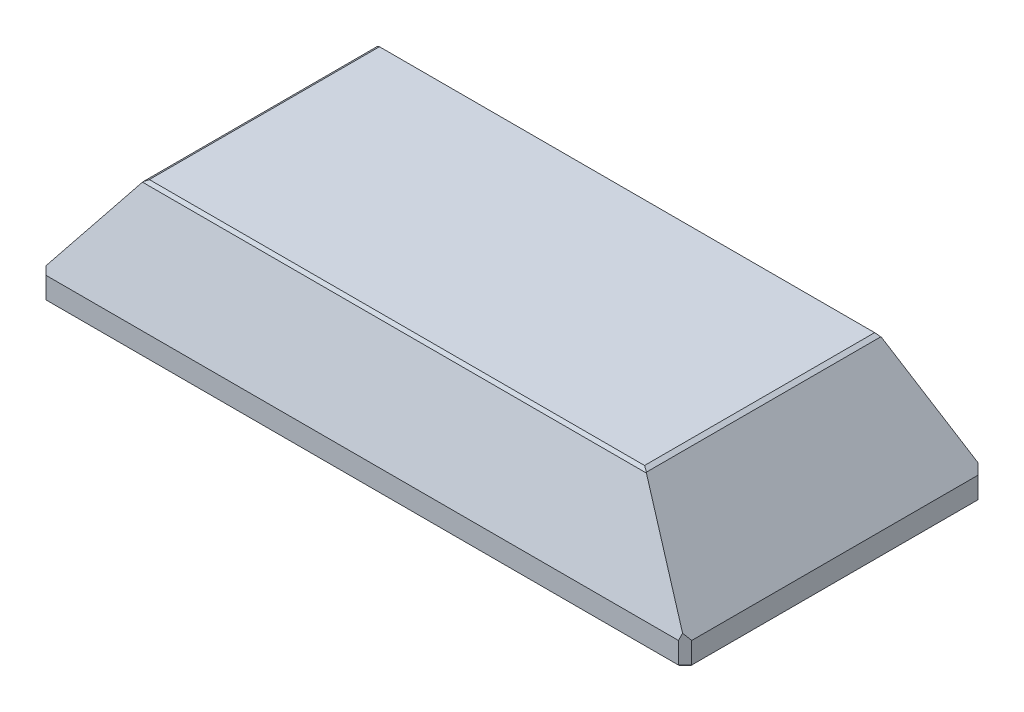
SolidWorks part; units mm, degrees
ref_plane "Front Plane" through (0, 0, 0) normal (0, 0, 1) x (1, 0, 0)
ref_plane "Top Plane" through (0, 0, 0) normal (0, 1, 0) x (1, 0, 0)
ref_plane "Right Plane" through (0, 0, 0) normal (1, 0, 0) x (0, 0, -1)
sketch "Sketch1" plane through (0, 0, 0) normal (0, 1, 0) x (1, 0, 0)
  line L1 (-97, -45) -> (97, -45)
  line L2 (-97, -45) -> (-97, 45)
  line L3 (-97, 45) -> (97, 45)
  line L4 (97, -45) -> (97, 45)
  line L5 (-97, -45) -> (97, 45) construction
  line L6 (-97, 45) -> (97, -45) construction
  point P0 (0, 0)
  dimension "D1" = 194
  dimension "D2" = 90
ref_plane "Plane1" through (0, 37, 0) normal (0, 1, 0) x (1, 0, 0)
sketch "Sketch2" plane through (0, 37, 0) normal (0, 1, 0) x (1, 0, 0)
  line L1 (-75, -35) -> (75, -35)
  line L2 (-75, -35) -> (-75, 35)
  line L3 (-75, 35) -> (75, 35)
  line L4 (75, -35) -> (75, 35)
  line L5 (-75, -35) -> (75, 35) construction
  line L6 (-75, 35) -> (75, -35) construction
  point P0 (0, 0)
  dimension "D1" = 70
  dimension "D2" = 150
extrude "Boss-Extrude1" add sketch "Sketch1" along normal blind 7
sketch "Sketch3" plane through (0, 7, 0) normal (0, 1, 0) x (1, 0, 0)
  line L4 (97, -45) -> (97, 45)
  line L5 (97, 45) -> (-97, 45)
  line L6 (-97, 45) -> (-97, -45)
  line L7 (-97, -45) -> (97, -45)
  line L8 (97, -45) -> (97, 45)
  line L9 (97, 45) -> (-97, 45)
  line L10 (-97, 45) -> (-97, -45)
  line L11 (-97, -45) -> (97, -45)
  dimension "D1" = 0
loft "Loft2" add profiles "Sketch3", "Sketch2"
chamfer "Chamfer1" distance 2 angle 45 4 edges at (-97, 3.5, 45) (97, 3.5, 45) (97, 3.5, -45) (-97, 3.5, -45)
sketch "Sketch4" plane through (0, 0, 0) normal (0, -1, 0) x (1, 0, 0)
  line L0 (0, 45) -> (0, -45) construction
  line L1 (-95, 45) -> (95, 45) construction
  line L2 (95, -45) -> (-95, -45) construction
  line L3 (-40, -41.5) -> (40, -41.5) construction
  circle A0 centre (40, -41.5) radius 2.15
  circle A1 centre (-40, -41.5) radius 2.15
  point P9 (0, -41.5)
  dimension "D3" = 4.3
  dimension "D1" = 3.5
  dimension "D2" = 80
extrude "Cut-Extrude1" cut sketch "Sketch4" against normal blind 7
sketch "Sketch5" plane through (0, 0, 0) normal (0, -1, 0) x (1, 0, 0)
  line L1 (-75, -30) -> (75, -30)
  line L2 (-75, -30) -> (-75, 30)
  line L3 (-75, 30) -> (75, 30)
  line L4 (75, -30) -> (75, 30)
  line L5 (-75, -30) -> (75, 30) construction
  line L6 (-75, 30) -> (75, -30) construction
  point P0 (0, 0)
  dimension "D1" = 60
  dimension "D2" = 150
extrude "Cut-Extrude2" cut sketch "Sketch5" against normal offset from surface (36 mm away) 1 up to face at (0, 37, 0)
mirror "Mirror1" about plane through (0, 0, 0) normal (0, 0, 1) of "Cut-Extrude1"
sketch "Sketch6" plane through (0, 0, 0) normal (0, -1, 0) x (1, 0, 0)
  line L0 (75, 30) -> (75, -30) construction
  line L1 (-75, -32) -> (75, -32)
  line L2 (-75, -32) -> (-75, 32)
  line L3 (-75, 32) -> (75, 32)
  line L4 (75, -32) -> (75, 32)
  line L5 (-75, -32) -> (75, 32) construction
  line L6 (-75, 32) -> (75, -32) construction
  line L7 (75, 30) -> (-75, 30) construction
  point P0 (0, 0)
  dimension "D1" = 2
extrude "Cut-Extrude3" cut sketch "Sketch6" against normal offset from surface (32 mm away) 4 up to face at (0, 36, 0)
sketch "Sketch7" plane through (0, 0, 0) normal (0, -1, 0) x (1, 0, 0)
  line L0 (-75, -32) -> (75, -32) construction
  line L1 (-75, 32) -> (-81, 32)
  line L2 (-75, 32) -> (-75, -32)
  line L3 (-75, -32) -> (-81, -32)
  line L4 (-81, 32) -> (-81, -32)
  line L5 (0, 45) -> (0, -45) construction
  line L6 (-95, 45) -> (95, 45) construction
  line L7 (95, -45) -> (-95, -45) construction
  line L8 (81, 32) -> (81, -32)
  line L9 (75, -32) -> (81, -32)
  line L10 (75, 32) -> (75, -32)
  line L11 (75, 32) -> (81, 32)
  dimension "D1" = 6
extrude "Cut-Extrude4" cut sketch "Sketch7" against normal blind 4
sketch "Sketch8" plane through (0, 4, 0) normal (0, -1, 0) x (1, 0, 0)
  line L0 (-81, 0) -> (81, 0) construction
  line L1 (-81, 32) -> (-81, -32) construction
  line L2 (81, -32) -> (81, 32) construction
  line L3 (-78, -25) -> (-78, 25) construction
  line L4 (-81, 32) -> (-75, -32) construction
  line L5 (0, 32) -> (0, -32) construction
  line L6 (-75, 32) -> (75, 32) construction
  line L7 (-81, -32) -> (81, -32) construction
  circle A0 centre (-78, 25) radius 2.05
  circle A1 centre (-78, -25) radius 2.05
  circle A2 centre (78, -25) radius 2.05
  circle A3 centre (78, 25) radius 2.05
  point P9 (-78, 0)
  dimension "D1" = 4.1
  dimension "D2" = 50
extrude "Cut-Extrude5" cut sketch "Sketch8" against normal blind 6
chamfer "Chamfer2" distance 1 angle 20 4 edges
chamfer "Chamfer3" distance 0.6 angle 45 8 edges at (96, 0, -44) (97, 0, 0) (96, 0, 44) (0, 0, -45) (-96, 0, -44) (-97, 0, 0) (-96, 0, 44) (0, 0, 45)
sketch "Skizze1" plane through (0, 36, 0) normal (0, -1, 0) x (1, 0, 0)
  line L0 (0, 30) -> (0, -25) construction
  line L1 (-75, 30) -> (75, 30) construction
  line L2 (-75, 30) -> (75, 30) construction
  line L3 (75, 0) -> (-75, 0) construction
  line L4 (75, 30) -> (75, -30) construction
  line L5 (-75, -32) -> (-75, 32) construction
  line L6 (-27.0252, -17.5) -> (27.0252, -17.5)
  line L7 (-27.0252, 30) -> (27.0252, 30)
  line L8 (-27.0252, 30) -> (-27.0252, 17.5)
  line L9 (-27.0252, 17.5) -> (27.0252, 17.5)
  line L10 (27.0252, 30) -> (27.0252, 17.5)
  line L11 (27.0252, -30) -> (27.0252, -17.5)
  line L12 (-27.0252, -30) -> (27.0252, -30)
  line L13 (-27.0252, -30) -> (-27.0252, -17.5)
  line L14 (75, 32) -> (75, -32) construction
  line L15 (75, 10.7265) -> (35, 10.7265)
  line L16 (75, 10.7265) -> (75, -10.7265)
  line L17 (75, -10.7265) -> (35, -10.7265)
  line L18 (35, 10.7265) -> (35, -10.7265)
  line L23 (-75, -30) -> (-75, 30) construction
  point P29 (0, 17.5)
  dimension "D1" = 35
  dimension "D2" = 110
extrude "Aufsatz-Linear austragen1" add sketch "Skizze1" along normal blind 10
sketch "Skizze3" plane through (0, 36, 0) normal (0, -1, 0) x (-1, 0, 0)
  line L0 (75, -30) -> (75, -32) construction
  line L2 (75, -31) -> (75, -30)
  line L10 (27.0252, -30) -> (27.0252, -31)
  line L11 (27.0252, -31) -> (75, -31)
  line L12 (27.0252, -30) -> (75, -30)
  line L14 (0, -44.4) -> (0, 44.4) construction
  line L22 (-94.7515, -44.4) -> (94.7515, -44.4) construction
  line L23 (94.7515, 44.4) -> (-94.7515, 44.4) construction
  line L24 (96.4, 0) -> (-96.4, 0) construction
  line L25 (96.4, -42.7515) -> (96.4, 42.7515) construction
  line L26 (-96.4, 42.7515) -> (-96.4, -42.7515) construction
  line L27 (-27.0252, -30) -> (-27.0252, -31)
  line L28 (-27.0252, -30) -> (-75, -30)
  line L29 (-27.0252, -31) -> (-75, -31)
  line L30 (-75, -31) -> (-75, -30)
  line L31 (27.0252, 30) -> (27.0252, 31)
  line L32 (27.0252, 31) -> (75, 31)
  line L33 (27.0252, 30) -> (75, 30)
  line L34 (75, 31) -> (75, 30)
  line L35 (-75, 31) -> (-75, 30)
  line L36 (-27.0252, 31) -> (-75, 31)
  line L37 (-27.0252, 30) -> (-27.0252, 31)
  line L38 (-27.0252, 30) -> (-75, 30)
extrude "Schnitt-Linear austragen2" cut sketch "Skizze3" along normal up to surface (4 mm away) up to face at (0, 32, 30.6667)
sketch "Sketch9" plane through (0, 4, 0) normal (0, -1, 0) x (1, 0, 0)
  line L1 (-75, 32) -> (75, 32)
  line L2 (-75, 32) -> (-75, -32)
  line L3 (-75, -32) -> (75, -32)
  line L4 (75, 32) -> (75, -32)
extrude "Cut-Extrude6" cut sketch "Sketch9" against normal up to surface (32 mm away) up to face at (13.75, 36, 0)
chamfer "Chamfer4" distance 0.4 angle 45 4 edges at (-40, 0, -43.65) (40, 0, -43.65) (-40, 0, 43.65) (40, 0, 43.65)
